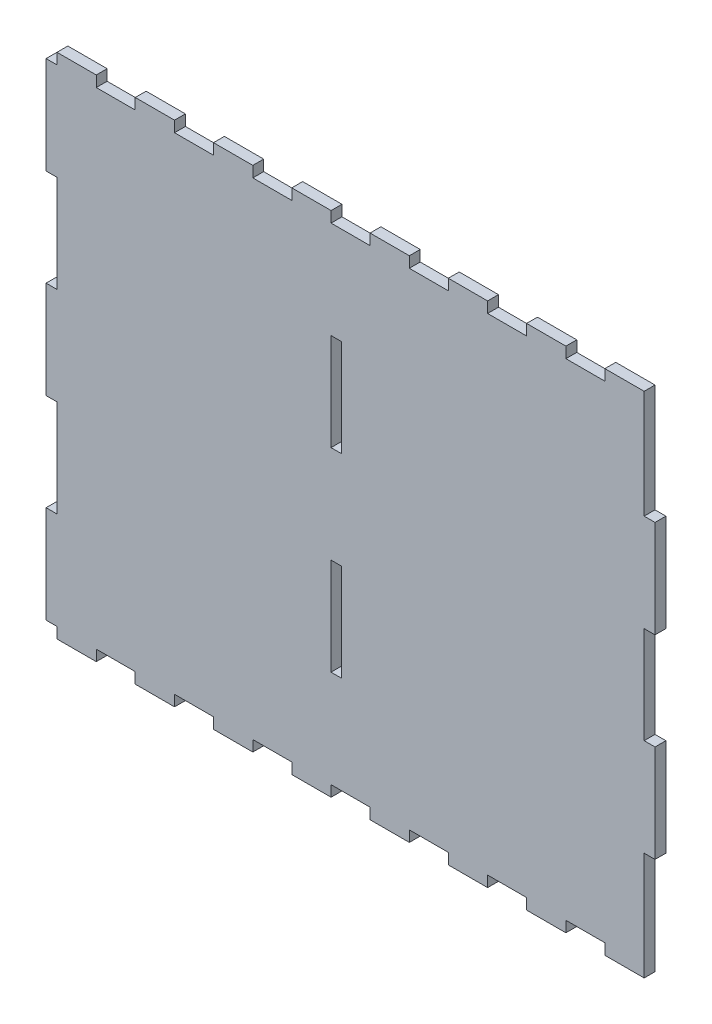
SolidWorks part; units mm, degrees
ref_plane "Front Plane" through (0, 0, 0) normal (0, 0, 1) x (1, 0, 0)
ref_plane "Top Plane" through (0, 0, 0) normal (0, 1, 0) x (1, 0, 0)
ref_plane "Right Plane" through (0, 0, 0) normal (1, 0, 0) x (0, 0, -1)
sketch "Sketch1" plane through (0, 0, 0) normal (0, 0, 1) x (1, 0, 0)
  line L0 (-200.4534, -13.9676) -> (-200.4534, -8.5676)
  line L1 (-239.3034, -13.9676) -> (52.0716, -13.9676)
  line L2 (-239.3034, -13.9676) -> (-239.3034, -255.2926)
  line L3 (-239.3034, -255.2926) -> (52.0716, -255.2926)
  line L4 (52.0716, -13.9676) -> (52.0716, -255.2926)
  line L5 (-239.3034, -13.9676) -> (-219.8784, -13.9676)
  line L6 (-239.3034, -13.9676) -> (-239.3034, -8.5676)
  line L7 (-239.3034, -8.5676) -> (-219.8784, -8.5676)
  line L8 (-219.8784, -13.9676) -> (-219.8784, -8.5676)
  line L9 (-200.4534, -8.5676) -> (-181.0284, -8.5676)
  line L10 (-181.0284, -13.9676) -> (-181.0284, -8.5676)
  line L11 (-161.6034, -13.9676) -> (-161.6034, -8.5676)
  line L12 (-161.6034, -8.5676) -> (-142.1784, -8.5676)
  line L13 (-142.1784, -13.9676) -> (-142.1784, -8.5676)
  line L14 (-122.7534, -13.9676) -> (-122.7534, -8.5676)
  line L15 (-122.7534, -8.5676) -> (-103.3284, -8.5676)
  line L16 (-103.3284, -13.9676) -> (-103.3284, -8.5676)
  line L17 (-83.9034, -13.9676) -> (-83.9034, -8.5676)
  line L18 (-83.9034, -8.5676) -> (-64.4784, -8.5676)
  line L19 (-64.4784, -13.9676) -> (-64.4784, -8.5676)
  line L20 (-45.0534, -13.9676) -> (-45.0534, -8.5676)
  line L21 (-45.0534, -8.5676) -> (-25.6284, -8.5676)
  line L22 (-25.6284, -13.9676) -> (-25.6284, -8.5676)
  line L23 (-6.2034, -13.9676) -> (-6.2034, -8.5676)
  line L24 (-6.2034, -8.5676) -> (13.2216, -8.5676)
  line L25 (13.2216, -13.9676) -> (13.2216, -8.5676)
  line L26 (32.6466, -13.9676) -> (32.6466, -8.5676)
  line L27 (32.6466, -8.5676) -> (52.0716, -8.5676)
  line L28 (52.0716, -13.9676) -> (52.0716, -8.5676)
  line L30 (-239.3034, -13.9676) -> (-244.7034, -13.9676)
  line L31 (-239.3034, -13.9676) -> (-239.3034, -62.2326)
  line L32 (-239.3034, -62.2326) -> (-244.7034, -62.2326)
  line L33 (-244.7034, -13.9676) -> (-244.7034, -62.2326)
  line L36 (-239.3034, -207.0276) -> (-244.7034, -207.0276)
  line L37 (-244.7034, -207.0276) -> (-244.7034, -255.2926)
  line L38 (-239.3034, -255.2926) -> (-244.7034, -255.2926)
  line L39 (52.0716, -158.7626) -> (57.4716, -158.7626)
  line L40 (52.0716, -62.2326) -> (57.4716, -62.2326)
  line L41 (52.0716, -62.2326) -> (52.0716, -110.4976)
  line L42 (52.0716, -110.4976) -> (57.4716, -110.4976)
  line L43 (57.4716, -62.2326) -> (57.4716, -110.4976)
  line L44 (57.4716, -158.7626) -> (57.4716, -207.0276)
  line L45 (52.0716, -207.0276) -> (57.4716, -207.0276)
  line L46 (-93.6159, -13.9676) -> (-93.6159, -94.2326) construction
  line L47 (-93.6159, -94.2326) -> (-93.6159, -255.2926) construction
  line L48 (-97.9534, -62.2326) -> (-103.3534, -62.2326)
  line L49 (-97.9534, -62.2326) -> (-97.9534, -110.4976)
  line L50 (-97.9534, -110.4976) -> (-103.3534, -110.4976)
  line L51 (-103.3534, -62.2326) -> (-103.3534, -110.4976)
  line L52 (-97.9534, -158.7626) -> (-103.3534, -158.7626)
  line L53 (-97.9534, -158.7626) -> (-97.9534, -207.0276)
  line L54 (-97.9534, -207.0276) -> (-103.3534, -207.0276)
  line L55 (-103.3534, -158.7626) -> (-103.3534, -207.0276)
  line L56 (52.0716, -134.6301) -> (-244.7034, -134.6301) construction
  line L57 (52.0716, -255.2926) -> (52.0716, -260.6926)
  line L58 (32.6466, -260.6926) -> (52.0716, -260.6926)
  line L59 (32.6466, -255.2926) -> (32.6466, -260.6926)
  line L60 (13.2216, -255.2926) -> (13.2216, -260.6926)
  line L61 (-6.2034, -260.6926) -> (13.2216, -260.6926)
  line L62 (-6.2034, -255.2926) -> (-6.2034, -260.6926)
  line L63 (-25.6284, -255.2926) -> (-25.6284, -260.6926)
  line L64 (-45.0534, -260.6926) -> (-25.6284, -260.6926)
  line L65 (-45.0534, -255.2926) -> (-45.0534, -260.6926)
  line L66 (-64.4784, -255.2926) -> (-64.4784, -260.6926)
  line L67 (-83.9034, -260.6926) -> (-64.4784, -260.6926)
  line L68 (-83.9034, -255.2926) -> (-83.9034, -260.6926)
  line L69 (-103.3284, -255.2926) -> (-103.3284, -260.6926)
  line L70 (-122.7534, -260.6926) -> (-103.3284, -260.6926)
  line L71 (-122.7534, -255.2926) -> (-122.7534, -260.6926)
  line L72 (-142.1784, -255.2926) -> (-142.1784, -260.6926)
  line L73 (-161.6034, -260.6926) -> (-142.1784, -260.6926)
  line L74 (-161.6034, -255.2926) -> (-161.6034, -260.6926)
  line L75 (-181.0284, -255.2926) -> (-181.0284, -260.6926)
  line L76 (-200.4534, -260.6926) -> (-181.0284, -260.6926)
  line L77 (-200.4534, -255.2926) -> (-200.4534, -260.6926)
  line L78 (-219.8784, -255.2926) -> (-219.8784, -260.6926)
  line L79 (-239.3034, -255.2926) -> (-239.3034, -260.6926)
  line L80 (-239.3034, -260.6926) -> (-219.8784, -260.6926)
  line L81 (-239.3034, -110.4976) -> (-244.7034, -110.4976)
  line L82 (-239.3034, -110.4976) -> (-239.3034, -158.7626)
  line L83 (-239.3034, -158.7626) -> (-244.7034, -158.7626)
  line L84 (-244.7034, -110.4976) -> (-244.7034, -158.7626)
  point P63 (0, 0)
  point P98 (-90.9159, -223.2926)
  dimension "D2" = 48.265
  dimension "D3" = 19.425
  dimension "D4" = 5.4
  dimension "D6" = 19.425
  dimension "D7" = 5.4
  dimension "D10" = 48.265
  dimension "D11" = 48.265
  dimension "D12" = 5.4
  dimension "D13" = 5.4
  dimension "D14" = 48.265
  dimension "D15" = 5.4
  dimension "D16" = 48.265
  dimension "D17" = 48.265
  dimension "D18" = 48.265
  dimension "D5" = 291.375
  dimension "D8" = 48.265
  dimension "D19" = 5.4
  dimension "D20" = 48.265
  dimension "D21" = 241.325
  dimension "D22" = 5.4
  dimension "D23" = 48.265
  dimension "D24" = 9.7375
  dimension "D9" = 2
extrude "Boss-Extrude1" add sketch "Sketch1" along normal blind 5.4
sketch "Sketch2" plane through (0, 0, 5.4) normal (0, 0, 1) x (1, 0, 0)
  line L92 (-103.3127, -110.4569) -> (-97.994, -110.4569)
  line L93 (-97.994, -110.4569) -> (-97.994, -62.2732)
  line L94 (-103.3127, -62.2732) -> (-103.3127, -110.4569)
  line L95 (-97.994, -62.2732) -> (-103.3127, -62.2732)
  line L96 (-103.3127, -110.4569) -> (-97.994, -110.4569)
  line L97 (-97.994, -110.4569) -> (-97.994, -62.2732)
  line L98 (-103.3127, -62.2732) -> (-103.3127, -110.4569)
  line L99 (-97.994, -62.2732) -> (-103.3127, -62.2732)
  line L104 (-103.3127, -206.9869) -> (-97.994, -206.9869)
  line L105 (-97.994, -206.9869) -> (-97.994, -158.8032)
  line L106 (-103.3127, -158.8032) -> (-103.3127, -206.9869)
  line L107 (-97.994, -158.8032) -> (-103.3127, -158.8032)
  line L108 (-103.3127, -206.9869) -> (-97.994, -206.9869)
  line L109 (-97.994, -206.9869) -> (-97.994, -158.8032)
  line L110 (-103.3127, -158.8032) -> (-103.3127, -206.9869)
  line L111 (-97.994, -158.8032) -> (-103.3127, -158.8032)
  line L160 (-239.344, -8.5269) -> (-239.344, -13.9269)
  line L161 (-239.344, -13.9269) -> (-244.744, -13.9269)
  line L162 (-244.744, -13.9269) -> (-244.744, -62.2732)
  line L163 (-244.744, -62.2732) -> (-239.344, -62.2732)
  line L164 (-239.344, -62.2732) -> (-239.344, -110.4569)
  line L165 (-239.344, -110.4569) -> (-244.744, -110.4569)
  line L166 (-244.744, -110.4569) -> (-244.744, -158.8032)
  line L167 (-244.744, -158.8032) -> (-239.344, -158.8032)
  line L168 (-239.344, -158.8032) -> (-239.344, -206.9869)
  line L169 (-239.344, -206.9869) -> (-244.744, -206.9869)
  line L170 (-244.744, -206.9869) -> (-244.744, -255.3332)
  line L171 (-244.744, -255.3332) -> (-239.344, -255.3332)
  line L172 (-239.344, -255.3332) -> (-239.344, -260.7332)
  line L173 (-239.344, -260.7332) -> (-219.8377, -260.7332)
  line L174 (-219.8377, -260.7332) -> (-219.8377, -255.3332)
  line L175 (-219.8377, -255.3332) -> (-200.494, -255.3332)
  line L176 (-200.494, -255.3332) -> (-200.494, -260.7332)
  line L177 (-200.494, -260.7332) -> (-180.9877, -260.7332)
  line L178 (-180.9877, -260.7332) -> (-180.9877, -255.3332)
  line L179 (-180.9877, -255.3332) -> (-161.644, -255.3332)
  line L180 (-161.644, -255.3332) -> (-161.644, -260.7332)
  line L181 (-161.644, -260.7332) -> (-142.1377, -260.7332)
  line L182 (-142.1377, -260.7332) -> (-142.1377, -255.3332)
  line L183 (-142.1377, -255.3332) -> (-122.794, -255.3332)
  line L184 (-122.794, -255.3332) -> (-122.794, -260.7332)
  line L185 (-122.794, -260.7332) -> (-103.2877, -260.7332)
  line L186 (-103.2877, -260.7332) -> (-103.2877, -255.3332)
  line L187 (-103.2877, -255.3332) -> (-83.944, -255.3332)
  line L188 (-83.944, -255.3332) -> (-83.944, -260.7332)
  line L189 (-83.944, -260.7332) -> (-64.4377, -260.7332)
  line L190 (-64.4377, -260.7332) -> (-64.4377, -255.3332)
  line L191 (-64.4377, -255.3332) -> (-45.094, -255.3332)
  line L192 (-45.094, -255.3332) -> (-45.094, -260.7332)
  line L193 (-45.094, -260.7332) -> (-25.5877, -260.7332)
  line L194 (-25.5877, -260.7332) -> (-25.5877, -255.3332)
  line L195 (-25.5877, -255.3332) -> (-6.244, -255.3332)
  line L196 (-6.244, -255.3332) -> (-6.244, -260.7332)
  line L197 (-6.244, -260.7332) -> (13.2623, -260.7332)
  line L198 (13.2623, -260.7332) -> (13.2623, -255.3332)
  line L199 (13.2623, -255.3332) -> (32.606, -255.3332)
  line L200 (32.606, -255.3332) -> (32.606, -260.7332)
  line L201 (32.606, -260.7332) -> (52.1123, -260.7332)
  line L202 (52.1123, -260.7332) -> (52.1123, -207.0682)
  line L203 (52.1123, -207.0682) -> (57.5123, -207.0682)
  line L204 (57.5123, -207.0682) -> (57.5123, -158.7219)
  line L205 (57.5123, -158.7219) -> (52.1123, -158.7219)
  line L206 (52.1123, -158.7219) -> (52.1123, -110.5382)
  line L207 (52.1123, -110.5382) -> (57.5123, -110.5382)
  line L208 (57.5123, -110.5382) -> (57.5123, -62.1919)
  line L209 (57.5123, -62.1919) -> (52.1123, -62.1919)
  line L210 (52.1123, -62.1919) -> (52.1123, -8.5269)
  line L211 (52.1123, -8.5269) -> (32.606, -8.5269)
  line L212 (32.606, -8.5269) -> (32.606, -13.9269)
  line L213 (32.606, -13.9269) -> (13.2623, -13.9269)
  line L214 (13.2623, -13.9269) -> (13.2623, -8.5269)
  line L215 (13.2623, -8.5269) -> (-6.244, -8.5269)
  line L216 (-6.244, -8.5269) -> (-6.244, -13.9269)
  line L217 (-6.244, -13.9269) -> (-25.5877, -13.9269)
  line L218 (-25.5877, -13.9269) -> (-25.5877, -8.5269)
  line L219 (-25.5877, -8.5269) -> (-45.094, -8.5269)
  line L220 (-45.094, -8.5269) -> (-45.094, -13.9269)
  line L221 (-45.094, -13.9269) -> (-64.4377, -13.9269)
  line L222 (-64.4377, -13.9269) -> (-64.4377, -8.5269)
  line L223 (-64.4377, -8.5269) -> (-83.944, -8.5269)
  line L224 (-83.944, -8.5269) -> (-83.944, -13.9269)
  line L225 (-83.944, -13.9269) -> (-103.2877, -13.9269)
  line L226 (-103.2877, -13.9269) -> (-103.2877, -8.5269)
  line L227 (-103.2877, -8.5269) -> (-122.794, -8.5269)
  line L228 (-122.794, -8.5269) -> (-122.794, -13.9269)
  line L229 (-122.794, -13.9269) -> (-142.1377, -13.9269)
  line L230 (-142.1377, -13.9269) -> (-142.1377, -8.5269)
  line L231 (-142.1377, -8.5269) -> (-161.644, -8.5269)
  line L232 (-161.644, -8.5269) -> (-161.644, -13.9269)
  line L233 (-161.644, -13.9269) -> (-180.9877, -13.9269)
  line L234 (-180.9877, -13.9269) -> (-180.9877, -8.5269)
  line L235 (-180.9877, -8.5269) -> (-200.494, -8.5269)
  line L236 (-200.494, -8.5269) -> (-200.494, -13.9269)
  line L237 (-200.494, -13.9269) -> (-219.8377, -13.9269)
  line L238 (-219.8377, -13.9269) -> (-219.8377, -8.5269)
  line L239 (-219.8377, -8.5269) -> (-239.344, -8.5269)
  line L240 (-239.344, -8.5269) -> (-239.344, -13.9269)
  line L241 (-239.344, -13.9269) -> (-244.744, -13.9269)
  line L242 (-244.744, -13.9269) -> (-244.744, -62.2732)
  line L243 (-244.744, -62.2732) -> (-239.344, -62.2732)
  line L244 (-239.344, -62.2732) -> (-239.344, -110.4569)
  line L245 (-239.344, -110.4569) -> (-244.744, -110.4569)
  line L246 (-244.744, -110.4569) -> (-244.744, -158.8032)
  line L247 (-244.744, -158.8032) -> (-239.344, -158.8032)
  line L248 (-239.344, -158.8032) -> (-239.344, -206.9869)
  line L249 (-239.344, -206.9869) -> (-244.744, -206.9869)
  line L250 (-244.744, -206.9869) -> (-244.744, -255.3332)
  line L251 (-244.744, -255.3332) -> (-239.344, -255.3332)
  line L252 (-239.344, -255.3332) -> (-239.344, -260.7332)
  line L253 (-239.344, -260.7332) -> (-219.8377, -260.7332)
  line L254 (-219.8377, -260.7332) -> (-219.8377, -255.3332)
  line L255 (-219.8377, -255.3332) -> (-200.494, -255.3332)
  line L256 (-200.494, -255.3332) -> (-200.494, -260.7332)
  line L257 (-200.494, -260.7332) -> (-180.9877, -260.7332)
  line L258 (-180.9877, -260.7332) -> (-180.9877, -255.3332)
  line L259 (-180.9877, -255.3332) -> (-161.644, -255.3332)
  line L260 (-161.644, -255.3332) -> (-161.644, -260.7332)
  line L261 (-161.644, -260.7332) -> (-142.1377, -260.7332)
  line L262 (-142.1377, -260.7332) -> (-142.1377, -255.3332)
  line L263 (-142.1377, -255.3332) -> (-122.794, -255.3332)
  line L264 (-122.794, -255.3332) -> (-122.794, -260.7332)
  line L265 (-122.794, -260.7332) -> (-103.2877, -260.7332)
  line L266 (-103.2877, -260.7332) -> (-103.2877, -255.3332)
  line L267 (-103.2877, -255.3332) -> (-83.944, -255.3332)
  line L268 (-83.944, -255.3332) -> (-83.944, -260.7332)
  line L269 (-83.944, -260.7332) -> (-64.4377, -260.7332)
  line L270 (-64.4377, -260.7332) -> (-64.4377, -255.3332)
  line L271 (-64.4377, -255.3332) -> (-45.094, -255.3332)
  line L272 (-45.094, -255.3332) -> (-45.094, -260.7332)
  line L273 (-45.094, -260.7332) -> (-25.5877, -260.7332)
  line L274 (-25.5877, -260.7332) -> (-25.5877, -255.3332)
  line L275 (-25.5877, -255.3332) -> (-6.244, -255.3332)
  line L276 (-6.244, -255.3332) -> (-6.244, -260.7332)
  line L277 (-6.244, -260.7332) -> (13.2623, -260.7332)
  line L278 (13.2623, -260.7332) -> (13.2623, -255.3332)
  line L279 (13.2623, -255.3332) -> (32.606, -255.3332)
  line L280 (32.606, -255.3332) -> (32.606, -260.7332)
  line L281 (32.606, -260.7332) -> (52.1123, -260.7332)
  line L282 (52.1123, -260.7332) -> (52.1123, -207.0682)
  line L283 (52.1123, -207.0682) -> (57.5123, -207.0682)
  line L284 (57.5123, -207.0682) -> (57.5123, -158.7219)
  line L285 (57.5123, -158.7219) -> (52.1123, -158.7219)
  line L286 (52.1123, -158.7219) -> (52.1123, -110.5382)
  line L287 (52.1123, -110.5382) -> (57.5123, -110.5382)
  line L288 (57.5123, -110.5382) -> (57.5123, -62.1919)
  line L289 (57.5123, -62.1919) -> (52.1123, -62.1919)
  line L290 (52.1123, -62.1919) -> (52.1123, -8.5269)
  line L291 (52.1123, -8.5269) -> (32.606, -8.5269)
  line L292 (32.606, -8.5269) -> (32.606, -13.9269)
  line L293 (32.606, -13.9269) -> (13.2623, -13.9269)
  line L294 (13.2623, -13.9269) -> (13.2623, -8.5269)
  line L295 (13.2623, -8.5269) -> (-6.244, -8.5269)
  line L296 (-6.244, -8.5269) -> (-6.244, -13.9269)
  line L297 (-6.244, -13.9269) -> (-25.5877, -13.9269)
  line L298 (-25.5877, -13.9269) -> (-25.5877, -8.5269)
  line L299 (-25.5877, -8.5269) -> (-45.094, -8.5269)
  line L300 (-45.094, -8.5269) -> (-45.094, -13.9269)
  line L301 (-45.094, -13.9269) -> (-64.4377, -13.9269)
  line L302 (-64.4377, -13.9269) -> (-64.4377, -8.5269)
  line L303 (-64.4377, -8.5269) -> (-83.944, -8.5269)
  line L304 (-83.944, -8.5269) -> (-83.944, -13.9269)
  line L305 (-83.944, -13.9269) -> (-103.2877, -13.9269)
  line L306 (-103.2877, -13.9269) -> (-103.2877, -8.5269)
  line L307 (-103.2877, -8.5269) -> (-122.794, -8.5269)
  line L308 (-122.794, -8.5269) -> (-122.794, -13.9269)
  line L309 (-122.794, -13.9269) -> (-142.1377, -13.9269)
  line L310 (-142.1377, -13.9269) -> (-142.1377, -8.5269)
  line L311 (-142.1377, -8.5269) -> (-161.644, -8.5269)
  line L312 (-161.644, -8.5269) -> (-161.644, -13.9269)
  line L313 (-161.644, -13.9269) -> (-180.9877, -13.9269)
  line L314 (-180.9877, -13.9269) -> (-180.9877, -8.5269)
  line L315 (-180.9877, -8.5269) -> (-200.494, -8.5269)
  line L316 (-200.494, -8.5269) -> (-200.494, -13.9269)
  line L317 (-200.494, -13.9269) -> (-219.8377, -13.9269)
  line L318 (-219.8377, -13.9269) -> (-219.8377, -8.5269)
  line L319 (-219.8377, -8.5269) -> (-239.344, -8.5269)
  dimension "D1" = 0.0406
  dimension "D2" = 0.0406
  dimension "D3" = 0.0406
extrude "Boss-Extrude2" add sketch "Sketch2" against normal up to surface (5.4 mm away) up to face at (-101.0353, -134.6301, 0)
equation "\"Structure Height\"= 26"
